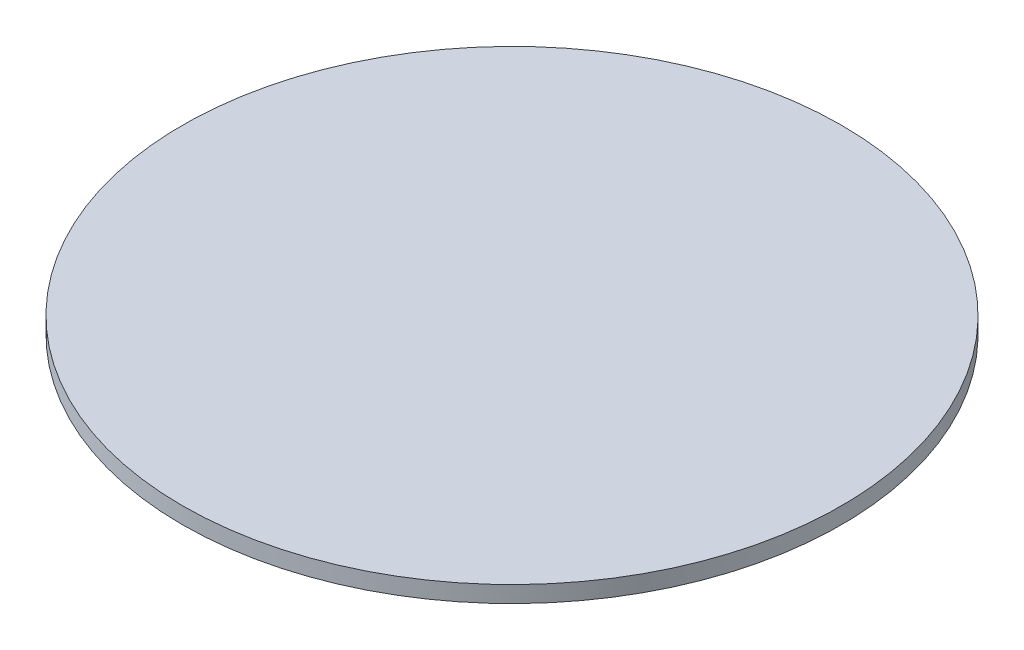
SolidWorks part; units mm, degrees
ref_plane "Plan de face" through (0, 0, 0) normal (0, 0, 1) x (1, 0, 0)
ref_plane "Plan de dessus" through (0, 0, 0) normal (0, 1, 0) x (1, 0, 0)
ref_plane "Plan de droite" through (0, 0, 0) normal (1, 0, 0) x (0, 0, -1)
sketch "Esquisse1" plane through (0, 0, 0) normal (0, 1, 0) x (1, 0, 0)
  circle A0 centre (0, 0) radius 20
  dimension "D1" = 40
extrude "Boss.-Extru.1" add sketch "Esquisse1" along normal blind 1
